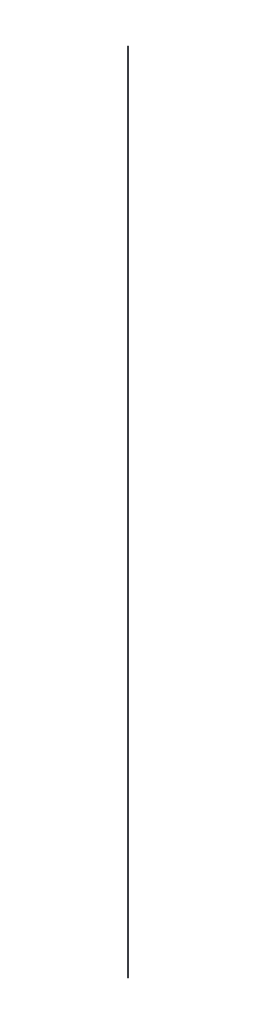
SolidWorks part; units mm, degrees
ref_plane "Front Plane" through (0, 0, 0) normal (0, 0, 1) x (1, 0, 0)
ref_plane "Top Plane" through (0, 0, 0) normal (0, 1, 0) x (1, 0, 0)
ref_plane "Right Plane" through (0, 0, 0) normal (1, 0, 0) x (0, 0, -1)
sketch "Sketch1" plane through (0, 0, 0) normal (0, 1, 0) x (1, 0, 0)
  circle A0 centre (0, 0) radius 0.1215
extrude "Boss-Extrude1" add sketch "Sketch1" along normal mid plane 500
